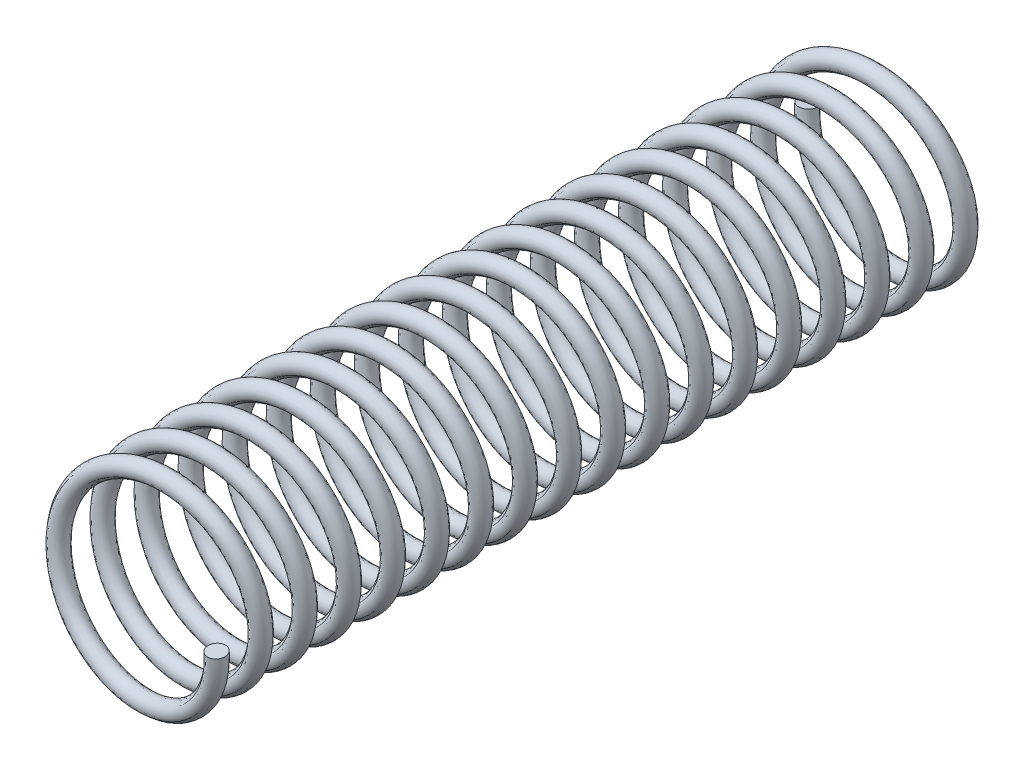
SolidWorks part; units mm, degrees
ref_plane "Front Plane" through (0, 0, 0) normal (0, 0, 1) x (1, 0, 0)
ref_plane "Top Plane" through (0, 0, 0) normal (0, 1, 0) x (1, 0, 0)
ref_plane "Right Plane" through (0, 0, 0) normal (1, 0, 0) x (0, 0, -1)
sketch "Sketch2" plane through (0, 0, 0) normal (0, 0, 1) x (1, 0, 0)
  circle A0 centre (0, 0) radius 1.9844
  dimension "D1" = 3.9688
curve "Helix/Spiral1" pitch 0.9725 height 17.018 turns 17.5
ref_plane "Plane1" through (1.9844, 0, 0) normal (0, -0.997, -0.0778) x (-1, 0, 0)
sketch "Sketch3" plane through (1.9844, 0, 0) normal (0, -0.997, -0.0778) x (-1, 0, 0)
  circle A0 centre (-0.0003, 0) radius 0.1984
  dimension "D1" = 0.3969
sweep "Sweep1" add profiles "Sketch3" path "Helix/Spiral1"
